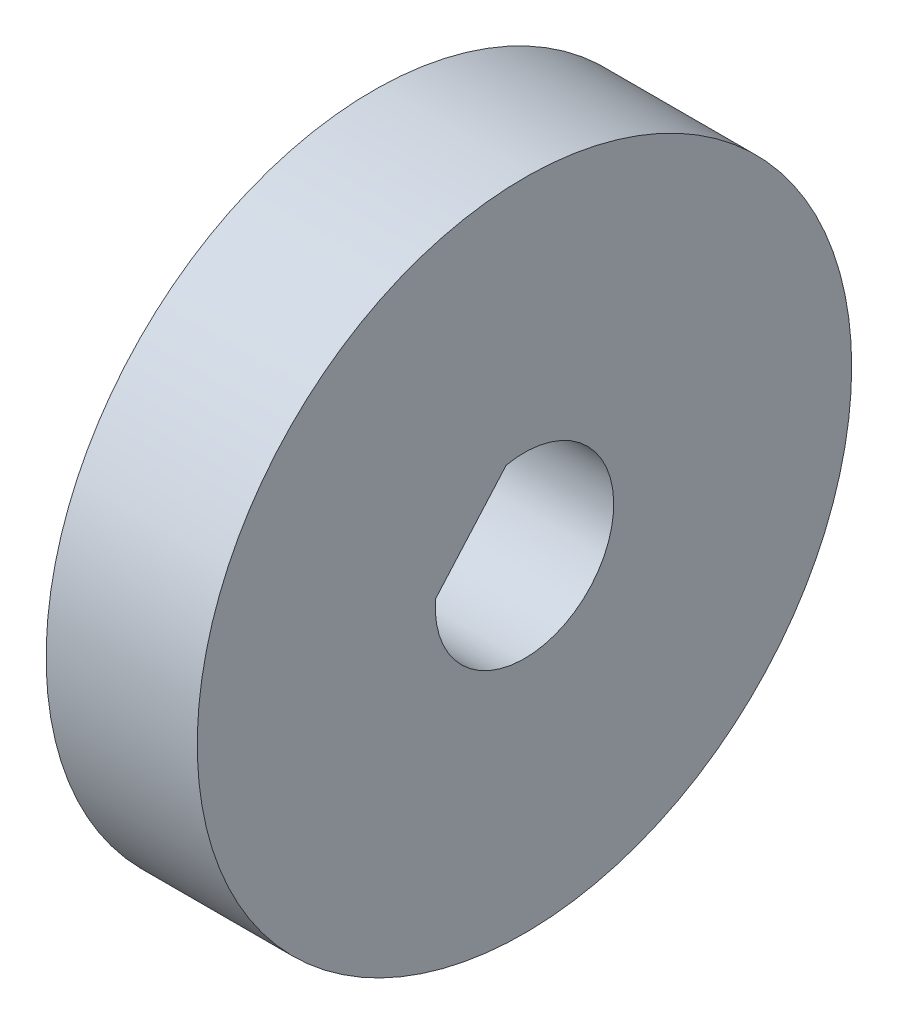
SolidWorks part; units mm, degrees
ref_plane "Front Plane" through (0, 0, 0) normal (0, 0, 1) x (1, 0, 0)
ref_plane "Top Plane" through (0, 0, 0) normal (0, 1, 0) x (1, 0, 0)
ref_plane "Right Plane" through (0, 0, 0) normal (1, 0, 0) x (0, 0, -1)
sketch "Sketch1" plane through (0, 0, 0) normal (1, 0, 0) x (0, 0, -1)
  circle A0 centre (0, 0) radius 11
  dimension "D1" = 22
extrude "Boss-Extrude1" add sketch "Sketch1" along normal blind 5.08
sketch "Sketch2" plane through (0, 0, 0) normal (-1, 0, 0) x (0, 0, 1)
  line L0 (0.6154, 2.9362) -> (2.9911, 0.2314) construction
  line L1 (0.6154, 2.9362) -> (2.9911, 0.2314)
  arc A0 (0.6154, 2.9362) -> (2.9911, 0.2314) centre (0, 0) ccw construction
  arc A1 (0.6154, 2.9362) -> (2.9911, 0.2314) centre (0, 0) ccw
extrude "Cut-Extrude1" cut sketch "Sketch2" against normal up to next
equation "\"MDF\"= 0.2in"
equation "\"D1@Boss-Extrude1\"=\"MDF\""
equation "\"TubeR\"= 0.8in"
equation "\"Foamcore\"= 0.2in"
